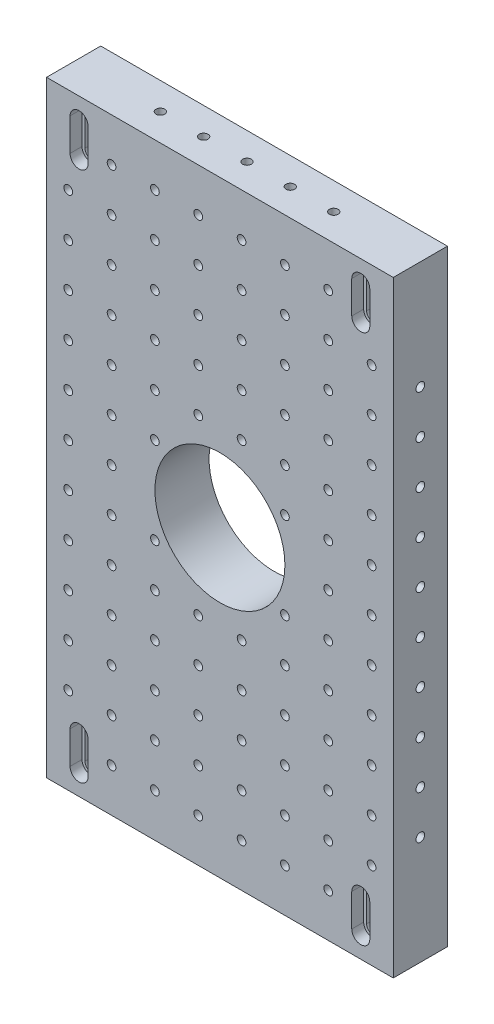
SolidWorks part; units mm, degrees
ref_plane "Front Plane" through (0, 0, 0) normal (0, 0, 1) x (1, 0, 0)
ref_plane "Top Plane" through (0, 0, 0) normal (0, 1, 0) x (1, 0, 0)
ref_plane "Right Plane" through (0, 0, 0) normal (1, 0, 0) x (0, 0, -1)
sketch "Sketch1" plane through (0, 0, 0) normal (0, 0, 1) x (1, 0, 0)
  line L1 (0, 0) -> (203.2, 0)
  line L2 (0, 0) -> (0, 355.6)
  line L3 (0, 355.6) -> (203.2, 355.6)
  line L4 (203.2, 0) -> (203.2, 355.6)
  circle A0 centre (101.6, 177.8) radius 38.1
extrude "Boss-Extrude1" add sketch "Sketch1" along normal blind 31.75
sketch "Sketch2" plane through (0, 0, 0) normal (0, -1, 0) x (1, 0, 0)
  line L0 (13.7668, 31.75) -> (13.7668, 24.765)
  line L1 (0, 31.75) -> (203.2, 31.75) construction
  line L2 (13.7668, 24.765) -> (15.4813, 24.765)
  line L3 (15.4813, 24.765) -> (15.4813, 0)
  line L4 (0, 0) -> (203.2, 0) construction
  line L5 (15.4813, 0) -> (22.6187, 0)
  line L6 (22.6187, 0) -> (22.6187, 24.765)
  line L7 (22.6187, 24.765) -> (24.3332, 24.765)
  line L8 (24.3332, 24.765) -> (24.3332, 31.75)
  line L9 (24.3332, 31.75) -> (13.7668, 31.75)
  line L10 (19.05, 0) -> (19.05, 31.75) construction
extrude "Cut-Extrude1" cut sketch "Sketch2" against normal blind 19.05 from offset 12.7 offset against normal yes
sketch "Sketch4" plane through (0, 31.75, 0) normal (0, -1, 0) x (1, 0, 0)
  line L0 (19.05, 0) -> (19.05, 31.75)
  line L1 (15.4813, 0) -> (22.6187, 0) construction
  line L2 (24.3332, 31.75) -> (13.7668, 31.75) construction
  line L3 (19.05, 31.75) -> (13.7668, 31.75)
  line L4 (13.7668, 31.75) -> (13.7668, 24.765)
  line L5 (13.7668, 24.765) -> (15.4813, 24.765)
  line L6 (15.4813, 24.765) -> (15.4813, 0)
  line L7 (15.4813, 0) -> (19.05, 0)
revolve "Cut-Revolve3" cut sketch "Sketch4" angle 360 about L0
sketch "Sketch6" plane through (0, 12.7, 0) normal (0, 1, 0) x (1, 0, 0)
  line L0 (19.05, 0) -> (19.05, -31.75)
  line L1 (15.4813, 0) -> (22.6187, 0) construction
  line L2 (24.3332, -31.75) -> (13.7668, -31.75) construction
  line L3 (19.05, -31.75) -> (24.3332, -31.75)
  line L4 (24.3332, -31.75) -> (24.3332, -24.765)
  line L5 (24.3332, -24.765) -> (22.6187, -24.765)
  line L6 (22.6187, -24.765) -> (22.6187, 0)
  line L7 (22.6187, 0) -> (19.05, 0)
revolve "Cut-Revolve4" cut sketch "Sketch6" angle 360 about L0
pattern_linear "LPattern1" count 2 spacing 311.15 along (0, 1, 0) count 2 spacing 165.1 along (1, 0, 0) of "Cut-Extrude1", "Cut-Revolve3", "Cut-Revolve4"
hole_wizard "1/4-20 Tapped Hole1" positions "Sketch8" profile "Sketch7" tap size "1/4-20" standard "Ansi Inch" end condition through all
sketch "Sketch8" plane through (0, 0, 31.75) normal (0, 0, 1) x (1, 0, 0)
  line L0 (0, 0) -> (203.2, 0) construction
  line L1 (0, 355.6) -> (0, 0) construction
  point P0 (12.7, 50.8)
sketch "Sketch7" plane through (12.7, 50.8, 31.75) normal (1, 0, 0) x (0, -1, 0)
  line L0 (0, 0) -> (0, 31.75)
  line L1 (0, 31.75) -> (2.5527, 31.75)
  line L2 (2.5527, 31.75) -> (2.5527, 0)
  line L5 (2.5527, 0) -> (0, 0)
  line L11 (0, -6.35) -> (0, 107.95) construction
  dimension "Thru Tap Drill Dia." = 5.1054
  dimension "Thru Tap Drill Depth" = 31.75
cosmetic thread "Hole Thread1" parameters "D2"=6.35
pattern_linear "LPattern2" count 12 spacing 25.4 along (0, 1, 0) count 8 spacing 25.4 along (1, 0, 0) skipping (5, 2), (5, 5), (11, 0), (11, 7) of "1/4-20 Tapped Hole1"
pattern_linear "LPattern3" count 2 spacing 25.4 along (0, -1, 0) count 8 spacing 25.4 along (1, 0, 0) skipping (1, 0), (1, 7) of "1/4-20 Tapped Hole1"
hole_wizard "1/4-20 Tapped Hole2" positions "Sketch10" profile "Sketch9" tap size "1/4-20" standard "Ansi Inch"
sketch "Sketch10" plane through (0, 0, 0) normal (-1, 0, 0) x (0, 0, 1)
  line L0 (31.75, 355.6) -> (0, 355.6) construction
  line L1 (0, 355.6) -> (0, 0) construction
  point P0 (15.875, 292.1)
  dimension "D1" = 63.5
  dimension "D2" = 15.875
sketch "Sketch9" plane through (0, 292.1, 15.875) normal (0, 1, 0) x (0, 0, 1)
  line L0 (0, 0) -> (0, 33.2838)
  line L1 (0, 33.2838) -> (2.5527, 31.75)
  line L2 (2.5527, 31.75) -> (2.5527, 0)
  line L5 (2.5527, 0) -> (0, 0)
  line L10 (0, 33.2838) -> (-2.5527, 31.75) construction
  line L11 (0, -6.35) -> (0, 107.95) construction
  dimension "Tap Drill Dia." = 5.1054
  dimension "Tap Drill Depth" = 31.75
  dimension "Drill Angle" = 118
cosmetic thread "Hole Thread2" parameters "D1"=25.4, "D2"=6.35
pattern_linear "LPattern4" count 10 spacing 25.4 along (0, -1, 0) of "1/4-20 Tapped Hole2"
hole_wizard "1/4-20 Tapped Hole3" positions "Sketch12" profile "Sketch14" tap size "1/4-20" standard "Ansi Inch"
sketch "Sketch12" plane through (203.2, -229.0211, 31.4791) normal (1, 0, 0) x (0, 0, -1)
  line L2 (-0.2709, 229.0211) -> (-0.2709, 584.6211) construction
  line L3 (-0.2709, 229.0211) -> (31.4791, 229.0211) construction
  point P0 (15.6041, 292.5211)
  dimension "D1" = 15.875
  dimension "D2" = 63.5
sketch "Sketch14" plane through (203.2, 63.5, 15.875) normal (0, 1, 0) x (0, 0, -1)
  line L0 (0, 0) -> (0, 33.2838)
  line L1 (0, 33.2838) -> (2.5527, 31.75)
  line L2 (2.5527, 31.75) -> (2.5527, 0)
  line L5 (2.5527, 0) -> (0, 0)
  line L10 (0, 33.2838) -> (-2.5527, 31.75) construction
  line L11 (0, -6.35) -> (0, 107.95) construction
  dimension "Tap Drill Dia." = 5.1054
  dimension "Tap Drill Depth" = 31.75
  dimension "Drill Angle" = 118
cosmetic thread "Hole Thread3" parameters "D1"=25.4, "D2"=6.35
pattern_linear "LPattern5" count 10 spacing 25.4 along (0, 1, 0) of "1/4-20 Tapped Hole3"
hole_wizard "1/4-20 Tapped Hole4" positions "Sketch16" profile "Sketch18" tap size "1/4-20" standard "Ansi Inch"
sketch "Sketch16" plane through (35.9486, 0, -278.1321) normal (0, -1, 0) x (1, 0, 0)
  line L2 (-35.9486, 309.8821) -> (167.2514, 309.8821) construction
  line L3 (-35.9486, 309.8821) -> (-35.9486, 278.1321) construction
  point P0 (14.8514, 294.0071)
  dimension "D1" = 15.875
  dimension "D2" = 50.8
sketch "Sketch18" plane through (50.8, 0, 15.875) normal (1, 0, 0) x (0, 0, -1)
  line L0 (0, 0) -> (0, 33.2838)
  line L1 (0, 33.2838) -> (2.5527, 31.75)
  line L2 (2.5527, 31.75) -> (2.5527, 0)
  line L5 (2.5527, 0) -> (0, 0)
  line L10 (0, 33.2838) -> (-2.5527, 31.75) construction
  line L11 (0, -6.35) -> (0, 107.95) construction
  dimension "Tap Drill Dia." = 5.1054
  dimension "Tap Drill Depth" = 31.75
  dimension "Drill Angle" = 118
cosmetic thread "Hole Thread4" parameters "D1"=25.4, "D2"=6.35
pattern_linear "LPattern6" count 5 spacing 25.4 along (1, 0, 0) of "1/4-20 Tapped Hole4"
hole_wizard "1/4-20 Tapped Hole5" positions "Sketch20" profile "Sketch22" tap size "1/4-20" standard "Ansi Inch"
sketch "Sketch20" plane through (169.6356, 355.6, -274.3412) normal (0, 1, 0) x (-1, 0, 0)
  line L2 (-33.5644, 306.0912) -> (169.6356, 306.0912) construction
  line L3 (-33.5644, 306.0912) -> (-33.5644, 274.3412) construction
  point P0 (17.2356, 290.2162)
  dimension "D1" = 15.875
  dimension "D2" = 50.8
sketch "Sketch22" plane through (152.4, 355.6, 15.875) normal (1, 0, 0) x (0, 0, 1)
  line L0 (0, 0) -> (0, 33.2838)
  line L1 (0, 33.2838) -> (2.5527, 31.75)
  line L2 (2.5527, 31.75) -> (2.5527, 0)
  line L5 (2.5527, 0) -> (0, 0)
  line L10 (0, 33.2838) -> (-2.5527, 31.75) construction
  line L11 (0, -6.35) -> (0, 107.95) construction
  dimension "Tap Drill Dia." = 5.1054
  dimension "Tap Drill Depth" = 31.75
  dimension "Drill Angle" = 118
cosmetic thread "Hole Thread5" parameters "D1"=25.4, "D2"=6.35
pattern_linear "LPattern7" count 5 spacing 25.4 along (-1, 0, 0) of "1/4-20 Tapped Hole5"
